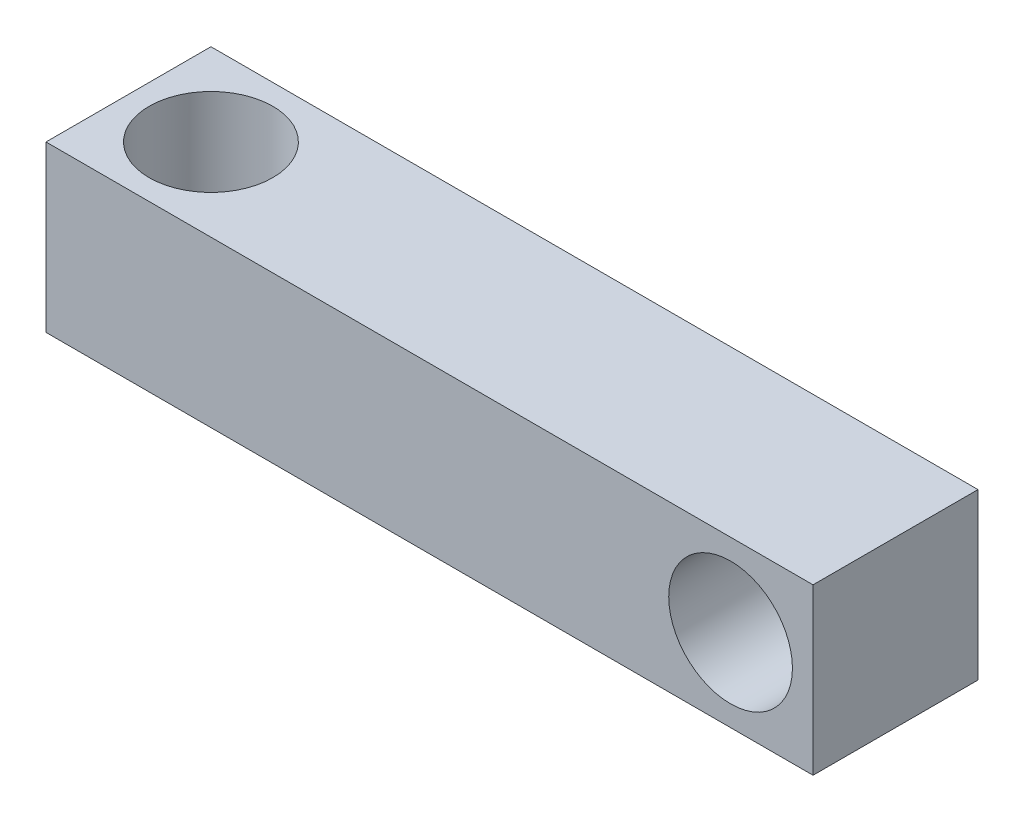
SolidWorks part; units mm, degrees
ref_plane "Alzado" through (0, 0, 0) normal (0, 0, 1) x (1, 0, 0)
ref_plane "Planta" through (0, 0, 0) normal (0, 1, 0) x (1, 0, 0)
ref_plane "Vista lateral" through (0, 0, 0) normal (1, 0, 0) x (0, 0, -1)
sketch "Croquis1" plane through (0, 0, 0) normal (0, 0, 1) x (1, 0, 0)
  line L0 (0, 11.7591) -> (46.5, 11.7591)
  line L1 (46.5, 11.7591) -> (46.5, -8.2409)
  line L2 (46.5, -8.2409) -> (-46.5, -8.2409)
  line L3 (-46.5, -8.2409) -> (-46.5, 11.7591)
  line L4 (-46.5, 11.7591) -> (0, 11.7591)
  dimension "D1" = 93
  dimension "D2" = 20
extrude "Saliente-Extruir1" add sketch "Croquis1" along normal mid plane 20
sketch "Croquis2" plane through (0, 0, 10) normal (0, 0, 1) x (1, 0, 0)
  line L0 (46.5, -8.2409) -> (46.5, 11.7591) construction
  circle A0 centre (36.5, 1.7591) radius 7.5
  dimension "D2" = 15
  dimension "D1" = 10
extrude "Cortar-Extruir1" cut sketch "Croquis2" against normal through all both and the other way through all
sketch "Croquis3" plane through (0, 11.7591, 0) normal (0, 1, 0) x (1, 0, 0)
  line L0 (-46.5, -10) -> (-46.5, 10) construction
  circle A0 centre (-36.5, 0) radius 7.5
  dimension "D2" = 15
  dimension "D1" = 10
extrude "Cortar-Extruir2" cut sketch "Croquis3" against normal through all both and the other way through all
